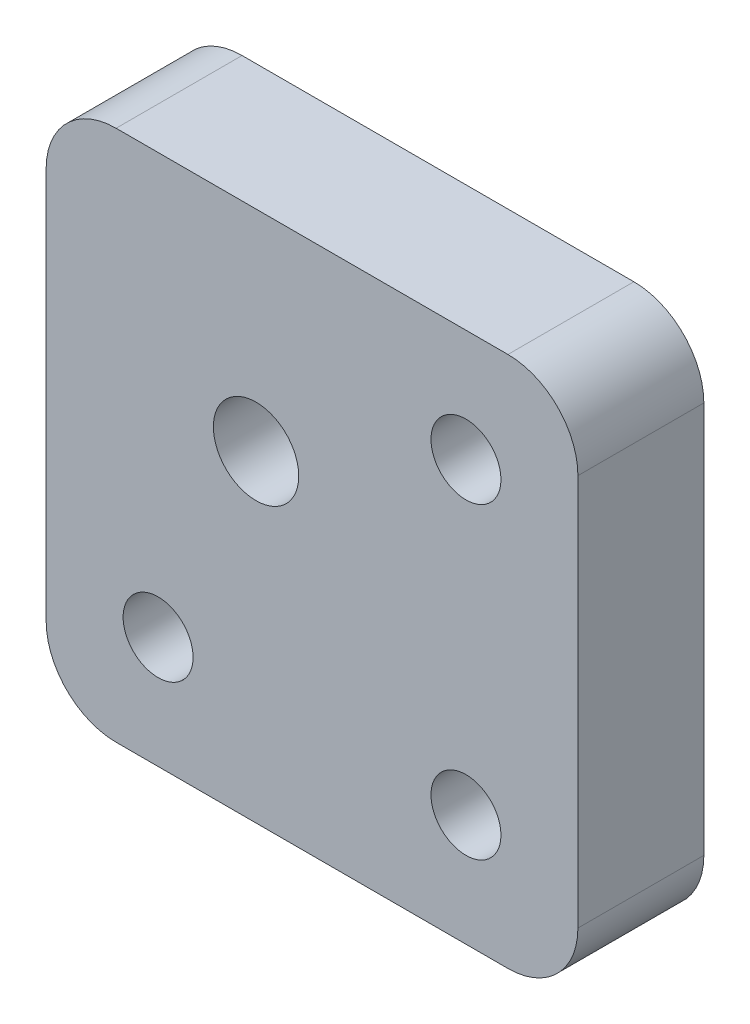
SolidWorks part; units mm, degrees
ref_plane "前视基准面" through (0, 0, 0) normal (0, 0, 1) x (1, 0, 0)
ref_plane "上视基准面" through (0, 0, 0) normal (0, 1, 0) x (1, 0, 0)
ref_plane "右视基准面" through (0, 0, 0) normal (1, 0, 0) x (0, 0, -1)
sketch "草图1" plane through (0, 0, 0) normal (0, 0, 1) x (1, 0, 0)
  line L0 (-2.1698, 45.9569) -> (-2.1698, -29.846) construction
  line L1 (-21.1698, 19.8398) -> (16.8302, 19.8398)
  line L2 (-21.1698, 19.8398) -> (-21.1698, -18.1602)
  line L3 (-21.1698, -18.1602) -> (16.8302, -18.1602)
  line L4 (16.8302, 19.8398) -> (16.8302, -18.1602)
  line L9 (-60.3251, 0.8398) -> (50.8197, 0.8398) construction
  line L11 (-13.1698, 11.8398) -> (8.8302, 11.8398) construction
  line L12 (-13.1698, 11.8398) -> (-13.1698, -10.1602) construction
  line L13 (-13.1698, -10.1602) -> (8.8302, -10.1602) construction
  line L14 (8.8302, 11.8398) -> (8.8302, -10.1602) construction
  circle A0 centre (8.8302, 11.8398) radius 2.5
  circle A1 centre (8.8302, -10.1602) radius 2.5
  circle A2 centre (-13.1698, -10.1602) radius 2.5
  circle A3 centre (-6.1698, 4.8398) radius 3.05
  dimension "D4" = 5
  dimension "D5" = 15
  dimension "D6" = 15
  dimension "D7" = 6.1
  dimension "D1" = 38
  dimension "D2" = 8
  dimension "D3" = 8
extrude "凸台-拉伸1" add sketch "草图1" along normal blind 9
fillet "圆角1" radius 5 4 edges at (-21.1698, 19.8398, 4.5) (-21.1698, -18.1602, 4.5) (16.8302, -18.1602, 4.5) (16.8302, 19.8398, 4.5)
